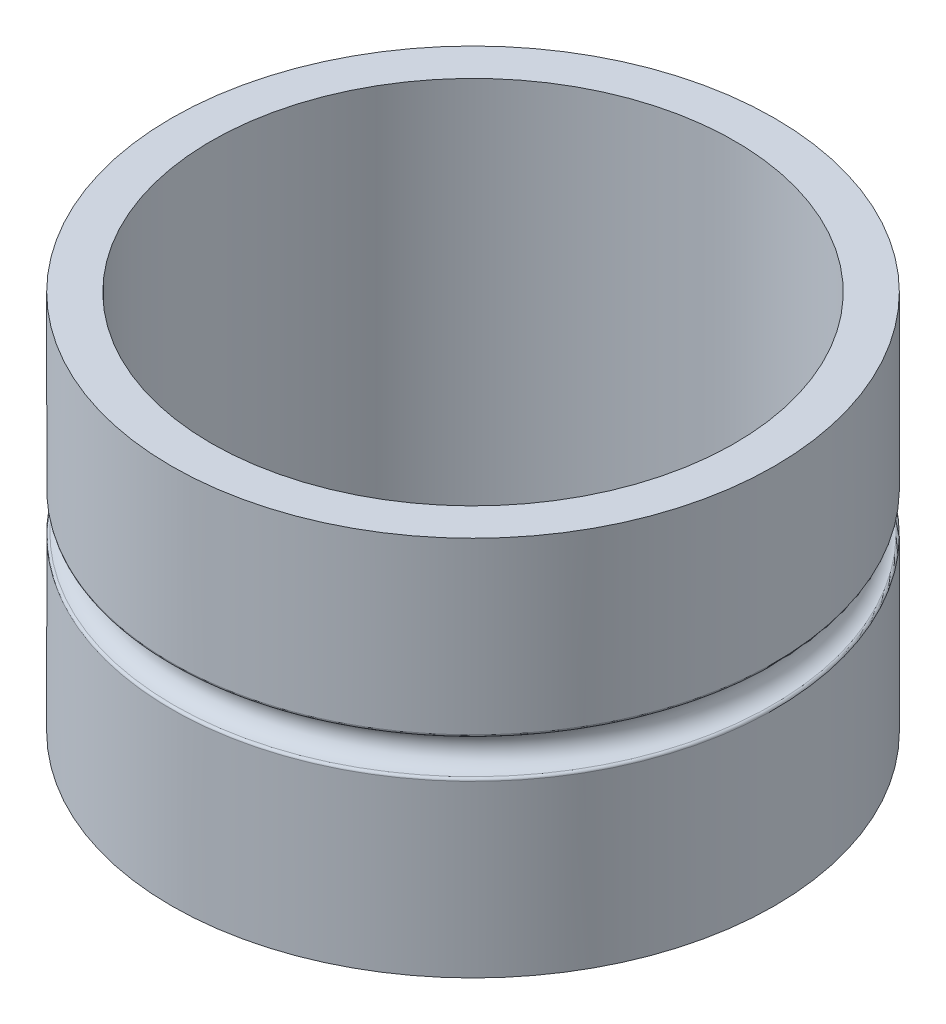
SolidWorks part; units mm, degrees
ref_plane "Front Plane" through (0, 0, 0) normal (0, 0, 1) x (1, 0, 0)
ref_plane "Top Plane" through (0, 0, 0) normal (0, 1, 0) x (1, 0, 0)
ref_plane "Right Plane" through (0, 0, 0) normal (1, 0, 0) x (0, 0, -1)
sketch "Sketch1" plane through (0, 0, 0) normal (0, 1, 0) x (1, 0, 0)
  circle A0 centre (0, 0) radius 60.325
  circle A1 centre (0, 0) radius 52.3875
  dimension "D1" = 120.65
  dimension "D2" = 7.9375
extrude "Boss-Extrude1" add sketch "Sketch1" along normal blind 76.2
sketch "Sketch2" plane through (0, 0, 0) normal (0, 0, 1) x (1, 0, 0)
  line L0 (60.325, 0) -> (60.325, 76.2) construction
  line L1 (60.325, 76.2) -> (-60.325, 76.2) construction
  line L2 (60.325, 0) -> (60.325, 76.2)
  arc A0 (60.325, 41.656) -> (60.325, 34.544) centre (60.325, 38.1) ccw
  dimension "D1" = 7.112
  dimension "D2" = 38.1
ref_axis "Axis1" through (0, 76.2, 0) along (0, -1, 0)
revolve "Cut-Revolve1" cut sketch "Sketch2" angle 360 about axis through (0, 76.2, 0) along (0, -1, 0)
fillet "Fillet1" radius 0.508 2 edges at (0, 34.544, 60.325) (0, 41.656, 60.325)
